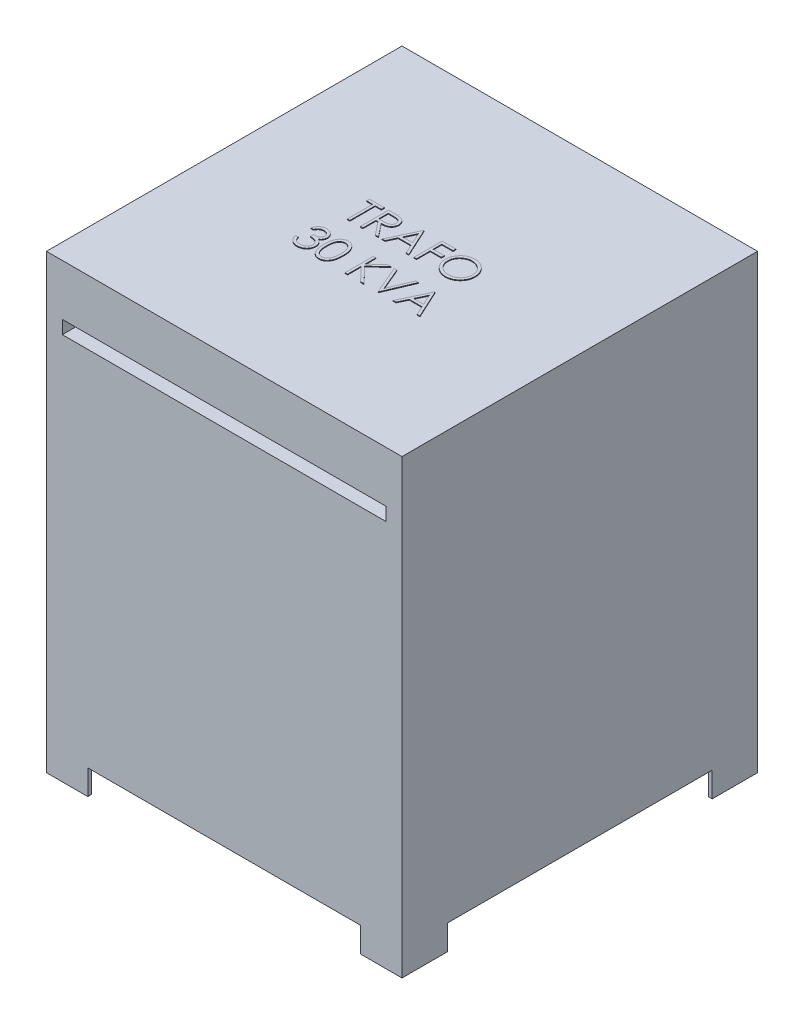
SolidWorks part; units mm, degrees
ref_plane "Alzado" through (0, 0, 0) normal (0, 0, 1) x (1, 0, 0)
ref_plane "Planta" through (0, 0, 0) normal (0, 1, 0) x (1, 0, 0)
ref_plane "Vista lateral" through (0, 0, 0) normal (1, 0, 0) x (0, 0, -1)
sketch "Croquis1" plane through (0, 0, 0) normal (0, 1, 0) x (1, 0, 0)
  line L1 (0, 0) -> (500, 0)
  line L2 (0, 0) -> (0, -500)
  line L3 (0, -500) -> (500, -500)
  line L4 (500, 0) -> (500, -500)
  dimension "D1" = 500
  dimension "D2" = 500
extrude "Saliente-Extruir1" add sketch "Croquis1" along normal blind 600
sketch "Croquis2" plane through (0, 0, 500) normal (0, 0, 1) x (1, 0, 0)
  line L1 (22.3866, 528.2789) -> (477.6134, 528.2789)
  line L2 (22.3866, 528.2789) -> (22.3866, 509.6439)
  line L3 (22.3866, 509.6439) -> (477.6134, 509.6439)
  line L4 (477.6134, 528.2789) -> (477.6134, 509.6439)
  line L5 (22.3866, 528.2789) -> (477.6134, 509.6439) construction
  line L6 (22.3866, 509.6439) -> (477.6134, 528.2789) construction
  point P0 (250, 518.9614)
extrude "Cortar-Extruir1" cut sketch "Croquis2" against normal blind 20
sketch "Croquis3" plane through (0, 0, 0) normal (0, -1, 0) x (1, 0, 0)
  line L0 (500, 0) -> (500, 63.8332)
  line L1 (500, 500) -> (500, 0) construction
  line L2 (500, 0) -> (441.7758, 0)
  line L3 (500, 0) -> (0, 0) construction
  line L4 (495, 5) -> (441.7758, 5)
  line L5 (495, 5) -> (495, 63.8332)
  line L6 (500, 63.8332) -> (495, 63.8332)
  line L7 (441.7758, 5) -> (441.7758, 0)
  line L8 (250, 500) -> (250, 0) construction
  line L9 (0, 500) -> (500, 500) construction
  line L10 (250, 0) -> (250, 250) construction
  line L11 (250, 250) -> (500, 250) construction
  line L12 (58.2242, 5) -> (58.2242, 0)
  line L13 (0, 63.8332) -> (5, 63.8332)
  line L14 (5, 5) -> (5, 63.8332)
  line L15 (5, 5) -> (58.2242, 5)
  line L16 (0, 0) -> (58.2242, 0)
  line L17 (0, 0) -> (0, 63.8332)
  line L18 (441.7758, 495) -> (441.7758, 500)
  line L19 (500, 436.1668) -> (495, 436.1668)
  line L20 (495, 495) -> (495, 436.1668)
  line L21 (495, 495) -> (441.7758, 495)
  line L22 (500, 500) -> (441.7758, 500)
  line L23 (500, 500) -> (500, 436.1668)
  line L24 (0, 500) -> (0, 436.1668)
  line L25 (0, 500) -> (58.2242, 500)
  line L26 (5, 495) -> (58.2242, 495)
  line L27 (5, 495) -> (5, 436.1668)
  line L28 (0, 436.1668) -> (5, 436.1668)
  line L29 (58.2242, 495) -> (58.2242, 500)
  dimension "D1" = 5
extrude "Saliente-Extruir2" add sketch "Croquis3" along normal blind 35
sketch "Croquis4" plane through (0, 600, 0) normal (0, 1, 0) x (1, 0, 0)
  line L0 (0, -250) -> (500, -250) construction
  line L1 (0, 0) -> (0, -500) construction
  line L2 (500, -500) -> (500, 0) construction
  text T0 "TRAFO\r\n30 KVA" font "Century Gothic" height in points 150
extrude "Saliente-Extruir3" add sketch "Croquis4" along normal blind 1
